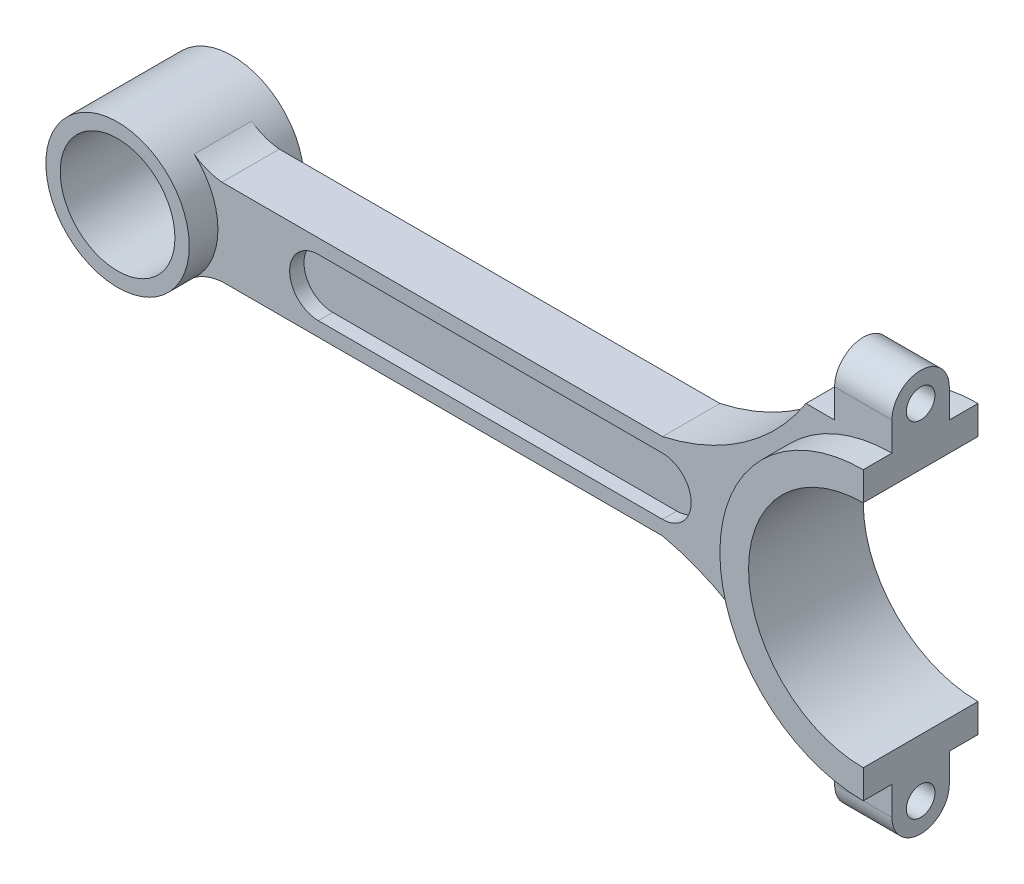
SolidWorks part; units mm, degrees
ref_plane "Front Plane" through (0, 0, 0) normal (0, 0, 1) x (1, 0, 0)
ref_plane "Top Plane" through (0, 0, 0) normal (0, 1, 0) x (1, 0, 0)
ref_plane "Right Plane" through (0, 0, 0) normal (1, 0, 0) x (0, 0, -1)
sketch "Sketch2" plane through (0, 0, 0) normal (0, 0, 1) x (1, 0, 0)
  line L0 (0, 0) -> (-165.1, 0) construction
  circle A0 centre (0, 0) radius 31.75
  circle A1 centre (-165.1, 0) radius 15.875
  dimension "D1" = 63.5
  dimension "D3" = 31.75
  dimension "D2" = 165.1
extrude "Boss-Extrude2" add sketch "Sketch2" along normal mid plane 25.4
sketch "Sketch3" plane through (0, 0, 12.7) normal (0, 0, 1) x (1, 0, 0)
  line L0 (0, 31.75) -> (-50.8, 31.75) construction
  line L1 (0, -31.75) -> (-50.8, -31.75) construction
  line L2 (31.75, 0) -> (-31.75, 0)
  line L3 (-50.8, 31.75) -> (-50.8, -31.75) construction
  line L4 (0, 31.75) -> (-19.05, 31.75)
  line L5 (0, 31.75) -> (0, -31.75)
  line L6 (0, -31.75) -> (-19.05, -31.75)
  line L8 (-50.8, 0) -> (-127, 0) construction
  line L10 (-154.4924, 11.8108) -> (-154.4924, -11.8108) construction
  line L12 (0, 9.525) -> (0, -9.525)
  line L15 (-148.343, 9.525) -> (-148.343, -9.525) construction
  line L16 (-165.1, 15.875) -> (-165.1, -15.875) construction
  line L17 (-180.975, 0) -> (-149.225, 0) construction
  line L18 (-50.8, 9.525) -> (-148.343, 9.525)
  line L19 (-50.8, -9.525) -> (-148.343, -9.525)
  line L20 (-154.4924, 11.8108) -> (-154.4924, -11.8108)
  circle A0 centre (0, 0) radius 31.75 construction
  circle A1 centre (-165.1, 0) radius 15.875 construction
  arc A2 (-50.8, 9.525) -> (-19.05, 31.75) centre (-61.8542, 59.1077) ccw
  arc A3 (-50.8, -9.525) -> (-19.05, -31.75) centre (-61.8542, -59.1077) cw
  arc A4 (-154.4924, 11.8108) -> (-148.343, 9.525) centre (-147.143, 22.1682) ccw
  arc A5 (-148.343, -9.525) -> (-154.4924, -11.8108) centre (-147.143, -22.1682) ccw
  arc A6 (-154.4924, 11.8108) -> (-149.225, 0) centre (-165.1, 0) ccw
  point P11 (0, 0)
  point P19 (-31.75, 0)
  dimension "D6" = 50.8
  dimension "D7" = 12.7
  dimension "D1" = 50.8
  dimension "D2" = 19.05
  dimension "D3" = 76.2
extrude "Boss-Extrude3" add sketch "Sketch3" against normal blind 12.7 from offset 6.35 separate body contours L20 A5 L19 A3 L6 L5 L4 A2 L18 A4 offset against normal yes
sketch "Sketch4" plane through (0, 0, 6.35) normal (0, 0, 1) x (1, 0, 0)
  line L0 (0, 0) -> (0, -31.75) construction
  line L1 (0, 0) -> (-50.8, 0) construction
  line L2 (-50.8, 0) -> (-127, 0) construction
  line L3 (-127, 6.35) -> (-50.8, 6.35)
  line L4 (-127, -6.35) -> (-50.8, -6.35)
  circle A0 centre (0, 0) radius 31.75 construction
  arc A1 (-50.8, -6.35) -> (-50.8, 6.35) centre (-50.8, 0) ccw
  arc A2 (-127, 6.35) -> (-127, -6.35) centre (-127, 0) ccw
  dimension "D2" = 12.7
  dimension "D1" = 50.8
extrude "Cut-Extrude1" cut sketch "Sketch4" against normal blind 3.175
mirror "Mirror1" about plane through (0, 0, 0) normal (0, 0, 1) of "Cut-Extrude1"
sketch "Sketch5" plane through (0, 0, 12.7) normal (0, 0, 1) x (1, 0, 0)
  line L0 (0, 31.75) -> (0, 25.4) construction
  line L1 (-165.1, 15.875) -> (-165.1, -15.875) construction
  line L2 (0, -25.4) -> (0, -31.75) construction
  line L3 (0, 31.75) -> (33.3961, 31.75)
  line L4 (0, 31.75) -> (0, 25.4)
  line L5 (0, -31.75) -> (33.3961, -31.75)
  line L6 (33.3961, 31.75) -> (33.3961, -31.75)
  line L7 (0, -25.4) -> (0, -31.75)
  arc A0 (0, 25.4) -> (0, -25.4) centre (0, 0) ccw
  circle A1 centre (-165.1, 0) radius 15.875 construction
  circle A2 centre (-165.1, 0) radius 12.7
  dimension "D1" = 50.8
  dimension "D2" = 25.4
extrude "Cut-Extrude2" cut sketch "Sketch5" against normal through all contours L3 L6 L5 L7 A0 L4 | A2
sketch "Sketch6" plane through (0, 0, 0) normal (1, 0, 0) x (0, 0, -1)
  line L1 (-6.35, 25.4) -> (6.35, 25.4)
  line L2 (-6.35, 25.4) -> (-6.35, 38.1)
  line L4 (6.35, 25.4) -> (6.35, 38.1)
  arc A0 (6.35, 38.1) -> (-6.35, 38.1) centre (0, 38.1) ccw
  point P6 (6.35, 31.75)
  dimension "D1" = 12.7
  dimension "D2" = 12.7
  dimension "D3" = 6.35
extrude "Boss-Extrude4" add sketch "Sketch6" against normal blind 12.7
mirror "Mirror2" about plane through (0, 0, 0) normal (0, 1, 0) of "Boss-Extrude4"
sketch "Sketch7" plane through (0, 0, 0) normal (1, 0, 0) x (0, 0, -1)
  line L0 (-6.35, 38.1) -> (6.35, 38.1) construction
  circle A0 centre (0, 38.1) radius 3.175
  dimension "D1" = 6.35
extrude "Cut-Extrude3" cut sketch "Sketch7" against normal blind 12.7
mirror "Mirror3" about plane through (0, 0, 0) normal (0, 1, 0) of "Cut-Extrude3"
